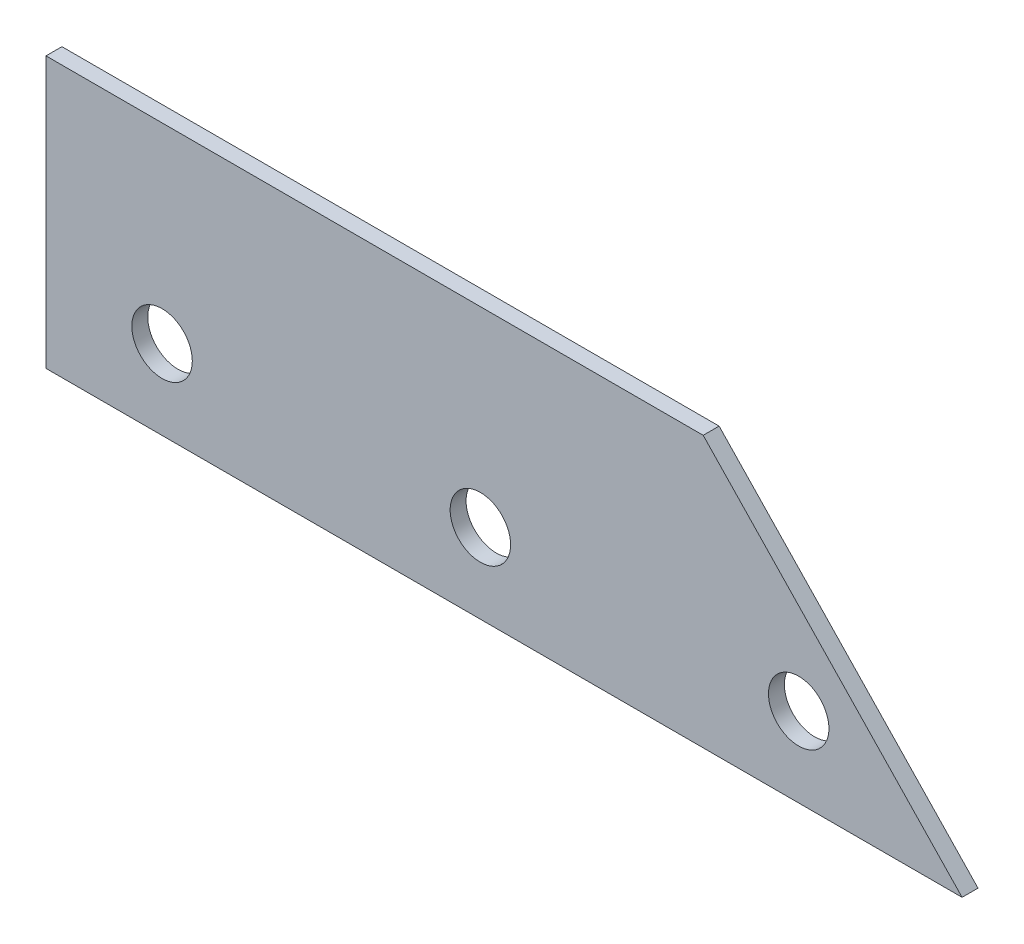
SolidWorks part; units mm, degrees
ref_plane "Спереди" through (0, 0, 0) normal (0, 0, 1) x (1, 0, 0)
ref_plane "Сверху" through (0, 0, 0) normal (0, 1, 0) x (1, 0, 0)
ref_plane "Справа" through (0, 0, 0) normal (1, 0, 0) x (0, 0, -1)
sketch "Эскиз1" plane through (0, 0, 0) normal (0, 0, 1) x (1, 0, 0)
  line L0 (45.3014, 5.375) -> (102.8597, 5.375)
  line L1 (45.3014, 22.3839) -> (45.3014, 3.2425) construction
  line L2 (106.0241, 2.0662) -> (86.5935, 22.3839) construction
  line L3 (102.8597, 5.375) -> (86.5935, 22.3839)
  line L4 (86.5935, 22.3839) -> (45.3014, 22.3839)
  line L5 (45.3014, 22.3839) -> (45.3014, 5.375)
  line L7 (56.1877, 0.375) -> (105.3014, 0.375) construction
  circle A1 centre (92.5935, 10.375) radius 1.9
  circle A2 centre (92.5935, 10.375) radius 1.9
  circle A3 centre (72.5935, 10.375) radius 1.9
  circle A4 centre (72.5935, 10.375) radius 1.9
  circle A5 centre (52.5935, 10.375) radius 1.9
  circle A6 centre (52.5935, 10.375) radius 1.9
  dimension "D4" = 5
  dimension "D1" = 0
  dimension "D2" = 0
  dimension "D3" = 0
extrude "Бобышка-Вытянуть1" add sketch "Эскиз1" along normal blind 1
